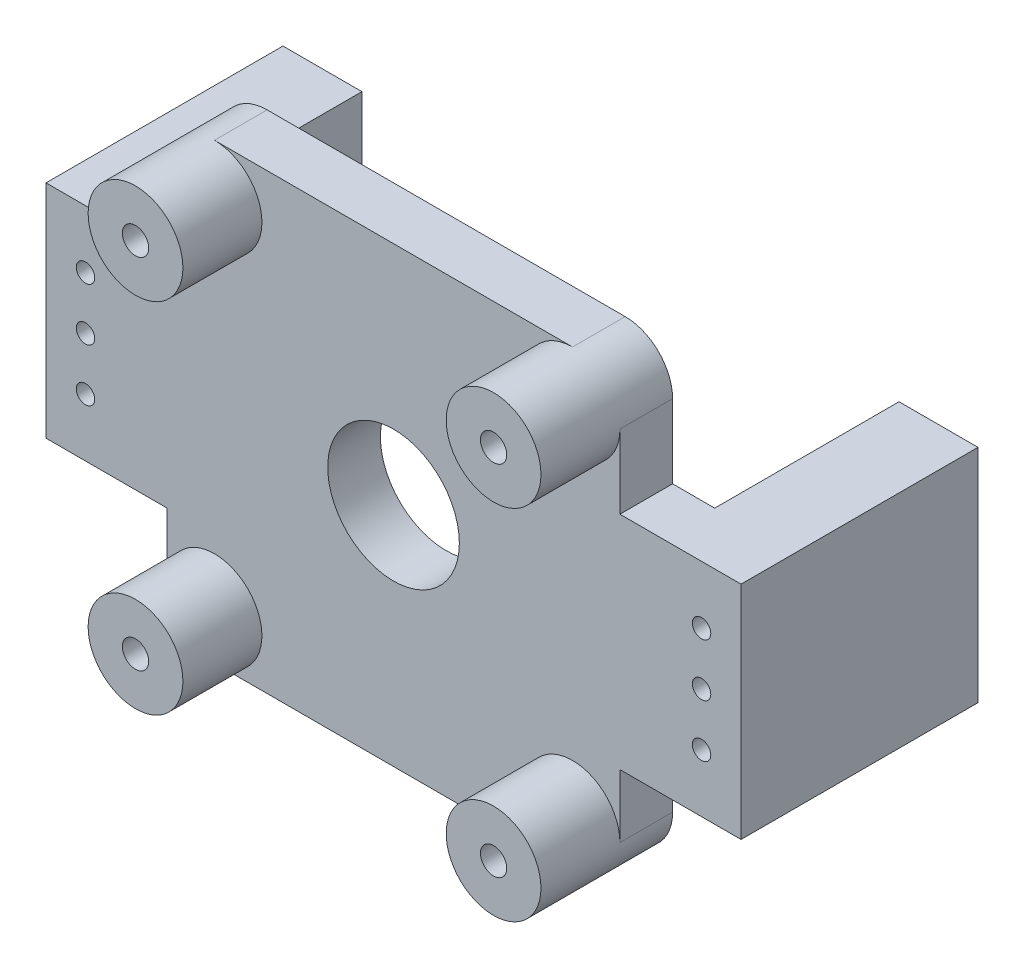
SolidWorks part; units mm, degrees
ref_plane "前视基准面" through (0, 0, 0) normal (0, 0, 1) x (1, 0, 0)
ref_plane "上视基准面" through (0, 0, 0) normal (0, 1, 0) x (1, 0, 0)
ref_plane "右视基准面" through (0, 0, 0) normal (1, 0, 0) x (0, 0, -1)
sketch "草图1" plane through (0, 0, 0) normal (0, 0, 1) x (1, 0, 0)
  line L1 (-43, 43) -> (43, 43)
  line L2 (-43, 43) -> (-43, -43)
  line L3 (-43, -43) -> (43, -43)
  line L4 (43, 43) -> (43, -43)
  circle A0 centre (-34, 34) radius 2
  circle A1 centre (34, 34) radius 2
  circle A2 centre (34, -34) radius 2
  circle A3 centre (-34, -34) radius 2
  dimension "D5" = 4
  dimension "D6" = 4
  dimension "D7" = 4
  dimension "D8" = 4
  dimension "D9" = 68
  dimension "D10" = 68
  dimension "D11" = 68
  dimension "D12" = 9
  dimension "D13" = 9
  dimension "D14" = 9
  dimension "D15" = 68
  dimension "D16" = 9
  dimension "D1" = 86
  dimension "D2" = 86
  dimension "D3" = 43
  dimension "D4" = 43
extrude "凸台-拉伸1" add sketch "草图1" along normal blind 10
fillet "圆角1" radius 5 4 edges at (-43, -43, 5) (43, -43, 5) (-43, 43, 5) (43, 43, 5)
sketch "草图2" plane through (0, 0, 10) normal (0, 0, 1) x (1, 0, 0)
  circle A0 centre (-34, 34) radius 9
  circle A1 centre (34, 34) radius 9
  circle A2 centre (34, -34) radius 9
  circle A3 centre (-34, -34) radius 9
  circle A4 centre (-34, 34) radius 2.5
  circle A5 centre (34, 34) radius 2.5
  circle A6 centre (34, -34) radius 2.5
  circle A7 centre (-34, -34) radius 2.5
  dimension "D1" = 18
  dimension "D2" = 18
  dimension "D3" = 18
  dimension "D4" = 18
  dimension "D5" = 5
  dimension "D6" = 5
  dimension "D7" = 5
  dimension "D8" = 5
extrude "凸台-拉伸2" add sketch "草图2" along normal blind 15
sketch "草图3" plane through (0, 0, 10) normal (0, 0, 1) x (1, 0, 0)
  circle A0 centre (0, 0) radius 12.5
  dimension "D1" = 25
extrude "切除-拉伸1" cut sketch "草图3" against normal blind 16
sketch "草图5" plane through (0, 0, 0) normal (0, 0, -1) x (-1, 0, 0)
  line L0 (5.7018, 29.4574) -> (7.4378, 39.3024)
  line L1 (4.717, 29.6311) -> (6.453, 39.4761)
  line L2 (0.5, 30) -> (0.5, 39.9969)
  line L3 (-0.5, 30) -> (-0.5, 39.9969)
  line L4 (4.717, 29.6311) -> (5.7018, 29.4574)
  line L5 (10.7305, 28.0198) -> (14.1496, 37.4138)
  line L6 (-0.5, 30) -> (0.5, 30)
  line L7 (9.7908, 28.3618) -> (13.2099, 37.7558)
  line L8 (9.7908, 28.3618) -> (10.7305, 28.0198)
  line L9 (15.433, 25.7308) -> (20.4315, 34.3883)
  line L10 (14.567, 26.2308) -> (19.5654, 34.8883)
  line L11 (14.567, 26.2308) -> (15.433, 25.7308)
  line L12 (19.6667, 22.6599) -> (26.0925, 30.318)
  line L13 (18.9006, 23.3027) -> (25.3265, 30.9608)
  line L14 (18.9006, 23.3027) -> (19.6667, 22.6599)
  line L15 (23.3027, 18.9006) -> (30.9608, 25.3265)
  line L16 (22.6599, 19.6667) -> (30.318, 26.0925)
  line L17 (22.6599, 19.6667) -> (23.3027, 18.9006)
  line L18 (26.2308, 14.567) -> (34.8883, 19.5654)
  line L19 (25.7308, 15.433) -> (34.3883, 20.4315)
  line L20 (25.7308, 15.433) -> (26.2308, 14.567)
  line L21 (28.3618, 9.7908) -> (37.7558, 13.2099)
  line L22 (28.0198, 10.7305) -> (37.4138, 14.1496)
  line L23 (28.0198, 10.7305) -> (28.3618, 9.7908)
  line L24 (29.6311, 4.717) -> (39.4761, 6.453)
  line L25 (29.4574, 5.7018) -> (39.3024, 7.4378)
  line L26 (29.4574, 5.7018) -> (29.6311, 4.717)
  line L27 (30, -0.5) -> (39.9969, -0.5)
  line L28 (30, 0.5) -> (39.9969, 0.5)
  line L29 (30, 0.5) -> (30, -0.5)
  line L30 (29.4574, -5.7018) -> (39.3024, -7.4378)
  line L31 (29.6311, -4.717) -> (39.4761, -6.453)
  line L32 (29.6311, -4.717) -> (29.4574, -5.7018)
  line L33 (28.0198, -10.7305) -> (37.4138, -14.1496)
  line L34 (28.3618, -9.7908) -> (37.7558, -13.2099)
  line L35 (28.3618, -9.7908) -> (28.0198, -10.7305)
  line L36 (25.7308, -15.433) -> (34.3883, -20.4315)
  line L37 (26.2308, -14.567) -> (34.8883, -19.5654)
  line L38 (26.2308, -14.567) -> (25.7308, -15.433)
  line L39 (22.6599, -19.6667) -> (30.318, -26.0925)
  line L40 (23.3027, -18.9006) -> (30.9608, -25.3265)
  line L41 (23.3027, -18.9006) -> (22.6599, -19.6667)
  line L42 (18.9006, -23.3027) -> (25.3265, -30.9608)
  line L43 (19.6667, -22.6599) -> (26.0925, -30.318)
  line L44 (19.6667, -22.6599) -> (18.9006, -23.3027)
  line L45 (14.567, -26.2308) -> (19.5654, -34.8883)
  line L46 (15.433, -25.7308) -> (20.4315, -34.3883)
  line L47 (15.433, -25.7308) -> (14.567, -26.2308)
  line L48 (9.7908, -28.3618) -> (13.2099, -37.7558)
  line L49 (10.7305, -28.0198) -> (14.1496, -37.4138)
  line L50 (10.7305, -28.0198) -> (9.7908, -28.3618)
  line L51 (4.717, -29.6311) -> (6.453, -39.4761)
  line L52 (5.7018, -29.4574) -> (7.4378, -39.3024)
  line L53 (5.7018, -29.4574) -> (4.717, -29.6311)
  line L54 (-0.5, -30) -> (-0.5, -39.9969)
  line L55 (0.5, -30) -> (0.5, -39.9969)
  line L56 (0.5, -30) -> (-0.5, -30)
  line L57 (-5.7018, -29.4574) -> (-7.4378, -39.3024)
  line L58 (-4.717, -29.6311) -> (-6.453, -39.4761)
  line L59 (-4.717, -29.6311) -> (-5.7018, -29.4574)
  line L60 (-10.7305, -28.0198) -> (-14.1496, -37.4138)
  line L61 (-9.7908, -28.3618) -> (-13.2099, -37.7558)
  line L62 (-9.7908, -28.3618) -> (-10.7305, -28.0198)
  line L63 (-15.433, -25.7308) -> (-20.4315, -34.3883)
  line L64 (-14.567, -26.2308) -> (-19.5654, -34.8883)
  line L65 (-14.567, -26.2308) -> (-15.433, -25.7308)
  line L66 (-19.6667, -22.6599) -> (-26.0925, -30.318)
  line L67 (-18.9006, -23.3027) -> (-25.3265, -30.9608)
  line L68 (-18.9006, -23.3027) -> (-19.6667, -22.6599)
  line L69 (-23.3027, -18.9006) -> (-30.9608, -25.3265)
  line L70 (-22.6599, -19.6667) -> (-30.318, -26.0925)
  line L71 (-22.6599, -19.6667) -> (-23.3027, -18.9006)
  line L72 (-26.2308, -14.567) -> (-34.8883, -19.5654)
  line L73 (-25.7308, -15.433) -> (-34.3883, -20.4315)
  line L74 (-25.7308, -15.433) -> (-26.2308, -14.567)
  line L75 (-28.3618, -9.7908) -> (-37.7558, -13.2099)
  line L76 (-28.0198, -10.7305) -> (-37.4138, -14.1496)
  line L77 (-28.0198, -10.7305) -> (-28.3618, -9.7908)
  line L78 (-29.6311, -4.717) -> (-39.4761, -6.453)
  line L79 (-29.4574, -5.7018) -> (-39.3024, -7.4378)
  line L80 (-29.4574, -5.7018) -> (-29.6311, -4.717)
  line L81 (-30, 0.5) -> (-39.9969, 0.5)
  line L82 (-30, -0.5) -> (-39.9969, -0.5)
  line L83 (-30, -0.5) -> (-30, 0.5)
  line L84 (-29.4574, 5.7018) -> (-39.3024, 7.4378)
  line L85 (-29.6311, 4.717) -> (-39.4761, 6.453)
  line L86 (-29.6311, 4.717) -> (-29.4574, 5.7018)
  line L87 (-28.0198, 10.7305) -> (-37.4138, 14.1496)
  line L88 (-28.3618, 9.7908) -> (-37.7558, 13.2099)
  line L89 (-28.3618, 9.7908) -> (-28.0198, 10.7305)
  line L90 (-25.7308, 15.433) -> (-34.3883, 20.4315)
  line L91 (-26.2308, 14.567) -> (-34.8883, 19.5654)
  line L92 (-26.2308, 14.567) -> (-25.7308, 15.433)
  line L93 (-22.6599, 19.6667) -> (-30.318, 26.0925)
  line L94 (-23.3027, 18.9006) -> (-30.9608, 25.3265)
  line L95 (-23.3027, 18.9006) -> (-22.6599, 19.6667)
  line L96 (-18.9006, 23.3027) -> (-25.3265, 30.9608)
  line L97 (-19.6667, 22.6599) -> (-26.0925, 30.318)
  line L98 (-19.6667, 22.6599) -> (-18.9006, 23.3027)
  line L99 (-14.567, 26.2308) -> (-19.5654, 34.8883)
  line L100 (-15.433, 25.7308) -> (-20.4315, 34.3883)
  line L101 (-15.433, 25.7308) -> (-14.567, 26.2308)
  line L102 (-9.7908, 28.3618) -> (-13.2099, 37.7558)
  line L103 (-10.7305, 28.0198) -> (-14.1496, 37.4138)
  line L104 (-10.7305, 28.0198) -> (-9.7908, 28.3618)
  line L105 (-4.717, 29.6311) -> (-6.453, 39.4761)
  line L106 (-5.7018, 29.4574) -> (-7.4378, 39.3024)
  line L107 (-5.7018, 29.4574) -> (-4.717, 29.6311)
  arc A0 (0.5, 39.9969) -> (-0.5, 39.9969) centre (0, 0) ccw
  arc A1 (7.4378, 39.3024) -> (6.453, 39.4761) centre (0, 0) ccw
  arc A2 (14.1496, 37.4138) -> (13.2099, 37.7558) centre (0, 0) ccw
  arc A3 (20.4315, 34.3883) -> (19.5654, 34.8883) centre (0, 0) ccw
  arc A4 (26.0925, 30.318) -> (25.3265, 30.9608) centre (0, 0) ccw
  arc A5 (30.9608, 25.3265) -> (30.318, 26.0925) centre (0, 0) ccw
  arc A6 (34.8883, 19.5654) -> (34.3883, 20.4315) centre (0, 0) ccw
  arc A7 (37.7558, 13.2099) -> (37.4138, 14.1496) centre (0, 0) ccw
  arc A8 (39.4761, 6.453) -> (39.3024, 7.4378) centre (0, 0) ccw
  arc A9 (39.9969, -0.5) -> (39.9969, 0.5) centre (0, 0) ccw
  arc A10 (39.3024, -7.4378) -> (39.4761, -6.453) centre (0, 0) ccw
  arc A11 (37.4138, -14.1496) -> (37.7558, -13.2099) centre (0, 0) ccw
  arc A12 (34.3883, -20.4315) -> (34.8883, -19.5654) centre (0, 0) ccw
  arc A13 (30.318, -26.0925) -> (30.9608, -25.3265) centre (0, 0) ccw
  arc A14 (25.3265, -30.9608) -> (26.0925, -30.318) centre (0, 0) ccw
  arc A15 (19.5654, -34.8883) -> (20.4315, -34.3883) centre (0, 0) ccw
  arc A16 (13.2099, -37.7558) -> (14.1496, -37.4138) centre (0, 0) ccw
  arc A17 (6.453, -39.4761) -> (7.4378, -39.3024) centre (0, 0) ccw
  arc A18 (-0.5, -39.9969) -> (0.5, -39.9969) centre (0, 0) ccw
  arc A19 (-7.4378, -39.3024) -> (-6.453, -39.4761) centre (0, 0) ccw
  arc A20 (-14.1496, -37.4138) -> (-13.2099, -37.7558) centre (0, 0) ccw
  arc A21 (-20.4315, -34.3883) -> (-19.5654, -34.8883) centre (0, 0) ccw
  arc A22 (-26.0925, -30.318) -> (-25.3265, -30.9608) centre (0, 0) ccw
  arc A23 (-30.9608, -25.3265) -> (-30.318, -26.0925) centre (0, 0) ccw
  arc A24 (-34.8883, -19.5654) -> (-34.3883, -20.4315) centre (0, 0) ccw
  arc A25 (-37.7558, -13.2099) -> (-37.4138, -14.1496) centre (0, 0) ccw
  arc A26 (-39.4761, -6.453) -> (-39.3024, -7.4378) centre (0, 0) ccw
  arc A27 (-39.9969, 0.5) -> (-39.9969, -0.5) centre (0, 0) ccw
  arc A28 (-39.3024, 7.4378) -> (-39.4761, 6.453) centre (0, 0) ccw
  arc A29 (-37.4138, 14.1496) -> (-37.7558, 13.2099) centre (0, 0) ccw
  arc A30 (-34.3883, 20.4315) -> (-34.8883, 19.5654) centre (0, 0) ccw
  arc A31 (-30.318, 26.0925) -> (-30.9608, 25.3265) centre (0, 0) ccw
  arc A32 (-25.3265, 30.9608) -> (-26.0925, 30.318) centre (0, 0) ccw
  arc A33 (-19.5654, 34.8883) -> (-20.4315, 34.3883) centre (0, 0) ccw
  arc A34 (-13.2099, 37.7558) -> (-14.1496, 37.4138) centre (0, 0) ccw
  arc A35 (-6.453, 39.4761) -> (-7.4378, 39.3024) centre (0, 0) ccw
  point P149 (0, 0)
  dimension "D1" = 80
  dimension "D2" = 36
extrude "凸台-拉伸3" [suppressed] add sketch "草图5" along normal blind 1
sketch "草图6" [suppressed] plane through (0, 0, 0) normal (0, 0, -1) x (-1, 0, 0)
  line L0 (2.5524, 34.9104) -> (2.9879, 39.8883)
  line L1 (8.5757, 33.9368) -> (9.869, 38.7634)
  line L2 (9.0587, 33.8074) -> (9.5416, 33.678)
  line L3 (9.5416, 33.678) -> (9.0587, 33.8074)
  line L4 (3.0505, 34.8668) -> (3.5485, 34.8232)
  line L5 (3.5485, 34.8232) -> (3.0505, 34.8668)
  line L6 (3.0505, 34.8668) -> (2.5524, 34.9104)
  line L7 (3.5485, 34.8232) -> (3.9841, 39.8011)
  line L8 (9.0587, 33.8074) -> (8.5757, 33.9368)
  line L9 (9.5416, 33.678) -> (10.8349, 38.5046)
  line L10 (14.3385, 31.9321) -> (16.4503, 36.4608)
  line L11 (14.7916, 31.7208) -> (15.2448, 31.5095)
  line L12 (15.2448, 31.5095) -> (14.7916, 31.7208)
  line L13 (14.7916, 31.7208) -> (14.3385, 31.9321)
  line L14 (15.2448, 31.5095) -> (17.3566, 36.0382)
  line L15 (19.6656, 28.9571) -> (22.5317, 33.0503)
  line L16 (20.0752, 28.6703) -> (20.4848, 28.3835)
  line L17 (20.4848, 28.3835) -> (20.0752, 28.6703)
  line L18 (20.0752, 28.6703) -> (19.6656, 28.9571)
  line L19 (20.4848, 28.3835) -> (23.3508, 32.4767)
  line L20 (24.3952, 25.1023) -> (27.9285, 28.6356)
  line L21 (24.7487, 24.7487) -> (25.1023, 24.3952)
  line L22 (25.1023, 24.3952) -> (24.7487, 24.7487)
  line L23 (24.7487, 24.7487) -> (24.3952, 25.1023)
  line L24 (25.1023, 24.3952) -> (28.6356, 27.9285)
  line L25 (28.3835, 20.4848) -> (32.4767, 23.3508)
  line L26 (28.6703, 20.0752) -> (28.9571, 19.6656)
  line L27 (28.9571, 19.6656) -> (28.6703, 20.0752)
  line L28 (28.6703, 20.0752) -> (28.3835, 20.4848)
  line L29 (28.9571, 19.6656) -> (33.0503, 22.5317)
  line L30 (31.5095, 15.2448) -> (36.0382, 17.3566)
  line L31 (31.7208, 14.7916) -> (31.9321, 14.3385)
  line L32 (31.9321, 14.3385) -> (31.7208, 14.7916)
  line L33 (31.7208, 14.7916) -> (31.5095, 15.2448)
  line L34 (31.9321, 14.3385) -> (36.4608, 16.4503)
  line L35 (33.678, 9.5416) -> (38.5046, 10.8349)
  line L36 (33.8074, 9.0587) -> (33.9368, 8.5757)
  line L37 (33.9368, 8.5757) -> (33.8074, 9.0587)
  line L38 (33.8074, 9.0587) -> (33.678, 9.5416)
  line L39 (33.9368, 8.5757) -> (38.7634, 9.869)
  line L40 (34.8232, 3.5485) -> (39.8011, 3.9841)
  line L41 (34.8668, 3.0505) -> (34.9104, 2.5524)
  line L42 (34.9104, 2.5524) -> (34.8668, 3.0505)
  line L43 (34.8668, 3.0505) -> (34.8232, 3.5485)
  line L44 (34.9104, 2.5524) -> (39.8883, 2.9879)
  line L45 (34.9104, -2.5524) -> (39.8883, -2.9879)
  line L46 (34.8668, -3.0505) -> (34.8232, -3.5485)
  line L47 (34.8232, -3.5485) -> (34.8668, -3.0505)
  line L48 (34.8668, -3.0505) -> (34.9104, -2.5524)
  line L49 (34.8232, -3.5485) -> (39.8011, -3.9841)
  line L50 (33.9368, -8.5757) -> (38.7634, -9.869)
  line L51 (33.8074, -9.0587) -> (33.678, -9.5416)
  line L52 (33.678, -9.5416) -> (33.8074, -9.0587)
  line L53 (33.8074, -9.0587) -> (33.9368, -8.5757)
  line L54 (33.678, -9.5416) -> (38.5046, -10.8349)
  line L55 (31.9321, -14.3385) -> (36.4608, -16.4503)
  line L56 (31.7208, -14.7916) -> (31.5095, -15.2448)
  line L57 (31.5095, -15.2448) -> (31.7208, -14.7916)
  line L58 (31.7208, -14.7916) -> (31.9321, -14.3385)
  line L59 (31.5095, -15.2448) -> (36.0382, -17.3566)
  line L60 (28.9571, -19.6656) -> (33.0503, -22.5317)
  line L61 (28.6703, -20.0752) -> (28.3835, -20.4848)
  line L62 (28.3835, -20.4848) -> (28.6703, -20.0752)
  line L63 (28.6703, -20.0752) -> (28.9571, -19.6656)
  line L64 (28.3835, -20.4848) -> (32.4767, -23.3508)
  line L65 (25.1023, -24.3952) -> (28.6356, -27.9285)
  line L66 (24.7487, -24.7487) -> (24.3952, -25.1023)
  line L67 (24.3952, -25.1023) -> (24.7487, -24.7487)
  line L68 (24.7487, -24.7487) -> (25.1023, -24.3952)
  line L69 (24.3952, -25.1023) -> (27.9285, -28.6356)
  line L70 (20.4848, -28.3835) -> (23.3508, -32.4767)
  line L71 (20.0752, -28.6703) -> (19.6656, -28.9571)
  line L72 (19.6656, -28.9571) -> (20.0752, -28.6703)
  line L73 (20.0752, -28.6703) -> (20.4848, -28.3835)
  line L74 (19.6656, -28.9571) -> (22.5317, -33.0503)
  line L75 (15.2448, -31.5095) -> (17.3566, -36.0382)
  line L76 (14.7916, -31.7208) -> (14.3385, -31.9321)
  line L77 (14.3385, -31.9321) -> (14.7916, -31.7208)
  line L78 (14.7916, -31.7208) -> (15.2448, -31.5095)
  line L79 (14.3385, -31.9321) -> (16.4503, -36.4608)
  line L80 (9.5416, -33.678) -> (10.8349, -38.5046)
  line L81 (9.0587, -33.8074) -> (8.5757, -33.9368)
  line L82 (8.5757, -33.9368) -> (9.0587, -33.8074)
  line L83 (9.0587, -33.8074) -> (9.5416, -33.678)
  line L84 (8.5757, -33.9368) -> (9.869, -38.7634)
  line L85 (3.5485, -34.8232) -> (3.9841, -39.8011)
  line L86 (3.0505, -34.8668) -> (2.5524, -34.9104)
  line L87 (2.5524, -34.9104) -> (3.0505, -34.8668)
  line L88 (3.0505, -34.8668) -> (3.5485, -34.8232)
  line L89 (2.5524, -34.9104) -> (2.9879, -39.8883)
  line L90 (-2.5524, -34.9104) -> (-2.9879, -39.8883)
  line L91 (-3.0505, -34.8668) -> (-3.5485, -34.8232)
  line L92 (-3.5485, -34.8232) -> (-3.0505, -34.8668)
  line L93 (-3.0505, -34.8668) -> (-2.5524, -34.9104)
  line L94 (-3.5485, -34.8232) -> (-3.9841, -39.8011)
  line L95 (-8.5757, -33.9368) -> (-9.869, -38.7634)
  line L96 (-9.0587, -33.8074) -> (-9.5416, -33.678)
  line L97 (-9.5416, -33.678) -> (-9.0587, -33.8074)
  line L98 (-9.0587, -33.8074) -> (-8.5757, -33.9368)
  line L99 (-9.5416, -33.678) -> (-10.8349, -38.5046)
  line L100 (-14.3385, -31.9321) -> (-16.4503, -36.4608)
  line L101 (-14.7916, -31.7208) -> (-15.2448, -31.5095)
  line L102 (-15.2448, -31.5095) -> (-14.7916, -31.7208)
  line L103 (-14.7916, -31.7208) -> (-14.3385, -31.9321)
  line L104 (-15.2448, -31.5095) -> (-17.3566, -36.0382)
  line L105 (-19.6656, -28.9571) -> (-22.5317, -33.0503)
  line L106 (-20.0752, -28.6703) -> (-20.4848, -28.3835)
  line L107 (-20.4848, -28.3835) -> (-20.0752, -28.6703)
  line L108 (-20.0752, -28.6703) -> (-19.6656, -28.9571)
  line L109 (-20.4848, -28.3835) -> (-23.3508, -32.4767)
  line L110 (-24.3952, -25.1023) -> (-27.9285, -28.6356)
  line L111 (-24.7487, -24.7487) -> (-25.1023, -24.3952)
  line L112 (-25.1023, -24.3952) -> (-24.7487, -24.7487)
  line L113 (-24.7487, -24.7487) -> (-24.3952, -25.1023)
  line L114 (-25.1023, -24.3952) -> (-28.6356, -27.9285)
  line L115 (-28.3835, -20.4848) -> (-32.4767, -23.3508)
  line L116 (-28.6703, -20.0752) -> (-28.9571, -19.6656)
  line L117 (-28.9571, -19.6656) -> (-28.6703, -20.0752)
  line L118 (-28.6703, -20.0752) -> (-28.3835, -20.4848)
  line L119 (-28.9571, -19.6656) -> (-33.0503, -22.5317)
  line L120 (-31.5095, -15.2448) -> (-36.0382, -17.3566)
  line L121 (-31.7208, -14.7916) -> (-31.9321, -14.3385)
  line L122 (-31.9321, -14.3385) -> (-31.7208, -14.7916)
  line L123 (-31.7208, -14.7916) -> (-31.5095, -15.2448)
  line L124 (-31.9321, -14.3385) -> (-36.4608, -16.4503)
  line L125 (-33.678, -9.5416) -> (-38.5046, -10.8349)
  line L126 (-33.8074, -9.0587) -> (-33.9368, -8.5757)
  line L127 (-33.9368, -8.5757) -> (-33.8074, -9.0587)
  line L128 (-33.8074, -9.0587) -> (-33.678, -9.5416)
  line L129 (-33.9368, -8.5757) -> (-38.7634, -9.869)
  line L130 (-34.8232, -3.5485) -> (-39.8011, -3.9841)
  line L131 (-34.8668, -3.0505) -> (-34.9104, -2.5524)
  line L132 (-34.9104, -2.5524) -> (-34.8668, -3.0505)
  line L133 (-34.8668, -3.0505) -> (-34.8232, -3.5485)
  line L134 (-34.9104, -2.5524) -> (-39.8883, -2.9879)
  line L135 (-34.9104, 2.5524) -> (-39.8883, 2.9879)
  line L136 (-34.8668, 3.0505) -> (-34.8232, 3.5485)
  line L137 (-34.8232, 3.5485) -> (-34.8668, 3.0505)
  line L138 (-34.8668, 3.0505) -> (-34.9104, 2.5524)
  line L139 (-34.8232, 3.5485) -> (-39.8011, 3.9841)
  line L140 (-33.9368, 8.5757) -> (-38.7634, 9.869)
  line L141 (-33.8074, 9.0587) -> (-33.678, 9.5416)
  line L142 (-33.678, 9.5416) -> (-33.8074, 9.0587)
  line L143 (-33.8074, 9.0587) -> (-33.9368, 8.5757)
  line L144 (-33.678, 9.5416) -> (-38.5046, 10.8349)
  line L145 (-31.9321, 14.3385) -> (-36.4608, 16.4503)
  line L146 (-31.7208, 14.7916) -> (-31.5095, 15.2448)
  line L147 (-31.5095, 15.2448) -> (-31.7208, 14.7916)
  line L148 (-31.7208, 14.7916) -> (-31.9321, 14.3385)
  line L149 (-31.5095, 15.2448) -> (-36.0382, 17.3566)
  line L150 (-28.9571, 19.6656) -> (-33.0503, 22.5317)
  line L151 (-28.6703, 20.0752) -> (-28.3835, 20.4848)
  line L152 (-28.3835, 20.4848) -> (-28.6703, 20.0752)
  line L153 (-28.6703, 20.0752) -> (-28.9571, 19.6656)
  line L154 (-28.3835, 20.4848) -> (-32.4767, 23.3508)
  line L155 (-25.1023, 24.3952) -> (-28.6356, 27.9285)
  line L156 (-24.7487, 24.7487) -> (-24.3952, 25.1023)
  line L157 (-24.3952, 25.1023) -> (-24.7487, 24.7487)
  line L158 (-24.7487, 24.7487) -> (-25.1023, 24.3952)
  line L159 (-24.3952, 25.1023) -> (-27.9285, 28.6356)
  line L160 (-20.4848, 28.3835) -> (-23.3508, 32.4767)
  line L161 (-20.0752, 28.6703) -> (-19.6656, 28.9571)
  line L162 (-19.6656, 28.9571) -> (-20.0752, 28.6703)
  line L163 (-20.0752, 28.6703) -> (-20.4848, 28.3835)
  line L164 (-19.6656, 28.9571) -> (-22.5317, 33.0503)
  line L165 (-15.2448, 31.5095) -> (-17.3566, 36.0382)
  line L166 (-14.7916, 31.7208) -> (-14.3385, 31.9321)
  line L167 (-14.3385, 31.9321) -> (-14.7916, 31.7208)
  line L168 (-14.7916, 31.7208) -> (-15.2448, 31.5095)
  line L169 (-14.3385, 31.9321) -> (-16.4503, 36.4608)
  line L170 (-9.5416, 33.678) -> (-10.8349, 38.5046)
  line L171 (-9.0587, 33.8074) -> (-8.5757, 33.9368)
  line L172 (-8.5757, 33.9368) -> (-9.0587, 33.8074)
  line L173 (-9.0587, 33.8074) -> (-9.5416, 33.678)
  line L174 (-8.5757, 33.9368) -> (-9.869, 38.7634)
  line L175 (-3.5485, 34.8232) -> (-3.9841, 39.8011)
  line L176 (-3.0505, 34.8668) -> (-2.5524, 34.9104)
  line L177 (-2.5524, 34.9104) -> (-3.0505, 34.8668)
  line L178 (-3.0505, 34.8668) -> (-3.5485, 34.8232)
  line L179 (-2.5524, 34.9104) -> (-2.9879, 39.8883)
  circle A0 centre (0, 0) radius 40
  circle A1 centre (0, 0) radius 41
  point P189 (0, 0)
  dimension "D2" = 36
  dimension "D1" = 1
extrude "凸台-拉伸4" [suppressed] add sketch "草图6" along normal blind 1 contours A1 A0 L43
sketch "草图7" plane through (0, 0, 0) normal (0, 0, -1) x (-1, 0, 0)
  line L0 (8.6331, 33.9186) -> (9.8664, 38.7641)
  line L1 (9.4828, 33.6909) -> (10.8375, 38.5039)
  line L2 (2.6121, 34.9024) -> (2.9852, 39.8884)
  line L3 (3.4883, 34.8257) -> (3.9867, 39.8008)
  line L4 (9.8664, 38.7641) -> (8.6331, 33.9186)
  line L5 (2.9852, 39.8884) -> (2.6121, 34.9024)
  line L6 (3.9867, 39.8008) -> (3.4883, 34.8257)
  line L7 (2.6121, 34.9024) -> (3.4883, 34.8257)
  line L8 (10.8375, 38.5039) -> (9.4828, 33.6909)
  line L9 (8.6331, 33.9186) -> (9.4828, 33.6909)
  line L10 (14.3919, 31.9041) -> (16.4478, 36.4619)
  line L11 (15.1891, 31.5324) -> (17.3589, 36.037)
  line L12 (16.4478, 36.4619) -> (14.3919, 31.9041)
  line L13 (17.3589, 36.037) -> (15.1891, 31.5324)
  line L14 (14.3919, 31.9041) -> (15.1891, 31.5324)
  line L15 (19.7133, 28.9203) -> (22.5295, 33.0518)
  line L16 (20.4339, 28.4158) -> (23.353, 32.4752)
  line L17 (22.5295, 33.0518) -> (19.7133, 28.9203)
  line L18 (23.353, 32.4752) -> (20.4339, 28.4158)
  line L19 (19.7133, 28.9203) -> (20.4339, 28.4158)
  line L20 (24.4358, 25.0578) -> (27.9266, 28.6375)
  line L21 (25.0578, 24.4358) -> (28.6375, 27.9266)
  line L22 (27.9266, 28.6375) -> (24.4358, 25.0578)
  line L23 (28.6375, 27.9266) -> (25.0578, 24.4358)
  line L24 (24.4358, 25.0578) -> (25.0578, 24.4358)
  line L25 (28.4158, 20.4339) -> (32.4752, 23.353)
  line L26 (28.9203, 19.7133) -> (33.0518, 22.5295)
  line L27 (32.4752, 23.353) -> (28.4158, 20.4339)
  line L28 (33.0518, 22.5295) -> (28.9203, 19.7133)
  line L29 (28.4158, 20.4339) -> (28.9203, 19.7133)
  line L30 (31.5324, 15.1891) -> (36.037, 17.3589)
  line L31 (31.9041, 14.3919) -> (36.4619, 16.4478)
  line L32 (36.037, 17.3589) -> (31.5324, 15.1891)
  line L33 (36.4619, 16.4478) -> (31.9041, 14.3919)
  line L34 (31.5324, 15.1891) -> (31.9041, 14.3919)
  line L35 (33.6909, 9.4828) -> (38.5039, 10.8375)
  line L36 (33.9186, 8.6331) -> (38.7641, 9.8664)
  line L37 (38.5039, 10.8375) -> (33.6909, 9.4828)
  line L38 (38.7641, 9.8664) -> (33.9186, 8.6331)
  line L39 (33.6909, 9.4828) -> (33.9186, 8.6331)
  line L40 (34.8257, 3.4883) -> (39.8008, 3.9867)
  line L41 (34.9024, 2.6121) -> (39.8884, 2.9852)
  line L42 (39.8008, 3.9867) -> (34.8257, 3.4883)
  line L43 (39.8884, 2.9852) -> (34.9024, 2.6121)
  line L44 (34.8257, 3.4883) -> (34.9024, 2.6121)
  line L45 (34.9024, -2.6121) -> (39.8884, -2.9852)
  line L46 (34.8257, -3.4883) -> (39.8008, -3.9867)
  line L47 (39.8884, -2.9852) -> (34.9024, -2.6121)
  line L48 (39.8008, -3.9867) -> (34.8257, -3.4883)
  line L49 (34.9024, -2.6121) -> (34.8257, -3.4883)
  line L50 (33.9186, -8.6331) -> (38.7641, -9.8664)
  line L51 (33.6909, -9.4828) -> (38.5039, -10.8375)
  line L52 (38.7641, -9.8664) -> (33.9186, -8.6331)
  line L53 (38.5039, -10.8375) -> (33.6909, -9.4828)
  line L54 (33.9186, -8.6331) -> (33.6909, -9.4828)
  line L55 (31.9041, -14.3919) -> (36.4619, -16.4478)
  line L56 (31.5324, -15.1891) -> (36.037, -17.3589)
  line L57 (36.4619, -16.4478) -> (31.9041, -14.3919)
  line L58 (36.037, -17.3589) -> (31.5324, -15.1891)
  line L59 (31.9041, -14.3919) -> (31.5324, -15.1891)
  line L60 (28.9203, -19.7133) -> (33.0518, -22.5295)
  line L61 (28.4158, -20.4339) -> (32.4752, -23.353)
  line L62 (33.0518, -22.5295) -> (28.9203, -19.7133)
  line L63 (32.4752, -23.353) -> (28.4158, -20.4339)
  line L64 (28.9203, -19.7133) -> (28.4158, -20.4339)
  line L65 (25.0578, -24.4358) -> (28.6375, -27.9266)
  line L66 (24.4358, -25.0578) -> (27.9266, -28.6375)
  line L67 (28.6375, -27.9266) -> (25.0578, -24.4358)
  line L68 (27.9266, -28.6375) -> (24.4358, -25.0578)
  line L69 (25.0578, -24.4358) -> (24.4358, -25.0578)
  line L70 (20.4339, -28.4158) -> (23.353, -32.4752)
  line L71 (19.7133, -28.9203) -> (22.5295, -33.0518)
  line L72 (23.353, -32.4752) -> (20.4339, -28.4158)
  line L73 (22.5295, -33.0518) -> (19.7133, -28.9203)
  line L74 (20.4339, -28.4158) -> (19.7133, -28.9203)
  line L75 (15.1891, -31.5324) -> (17.3589, -36.037)
  line L76 (14.3919, -31.9041) -> (16.4478, -36.4619)
  line L77 (17.3589, -36.037) -> (15.1891, -31.5324)
  line L78 (16.4478, -36.4619) -> (14.3919, -31.9041)
  line L79 (15.1891, -31.5324) -> (14.3919, -31.9041)
  line L80 (9.4828, -33.6909) -> (10.8375, -38.5039)
  line L81 (8.6331, -33.9186) -> (9.8664, -38.7641)
  line L82 (10.8375, -38.5039) -> (9.4828, -33.6909)
  line L83 (9.8664, -38.7641) -> (8.6331, -33.9186)
  line L84 (9.4828, -33.6909) -> (8.6331, -33.9186)
  line L85 (3.4883, -34.8257) -> (3.9867, -39.8008)
  line L86 (2.6121, -34.9024) -> (2.9852, -39.8884)
  line L87 (3.9867, -39.8008) -> (3.4883, -34.8257)
  line L88 (2.9852, -39.8884) -> (2.6121, -34.9024)
  line L89 (3.4883, -34.8257) -> (2.6121, -34.9024)
  line L90 (-2.6121, -34.9024) -> (-2.9852, -39.8884)
  line L91 (-3.4883, -34.8257) -> (-3.9867, -39.8008)
  line L92 (-2.9852, -39.8884) -> (-2.6121, -34.9024)
  line L93 (-3.9867, -39.8008) -> (-3.4883, -34.8257)
  line L94 (-2.6121, -34.9024) -> (-3.4883, -34.8257)
  line L95 (-8.6331, -33.9186) -> (-9.8664, -38.7641)
  line L96 (-9.4828, -33.6909) -> (-10.8375, -38.5039)
  line L97 (-9.8664, -38.7641) -> (-8.6331, -33.9186)
  line L98 (-10.8375, -38.5039) -> (-9.4828, -33.6909)
  line L99 (-8.6331, -33.9186) -> (-9.4828, -33.6909)
  line L100 (-14.3919, -31.9041) -> (-16.4478, -36.4619)
  line L101 (-15.1891, -31.5324) -> (-17.3589, -36.037)
  line L102 (-16.4478, -36.4619) -> (-14.3919, -31.9041)
  line L103 (-17.3589, -36.037) -> (-15.1891, -31.5324)
  line L104 (-14.3919, -31.9041) -> (-15.1891, -31.5324)
  line L105 (-19.7133, -28.9203) -> (-22.5295, -33.0518)
  line L106 (-20.4339, -28.4158) -> (-23.353, -32.4752)
  line L107 (-22.5295, -33.0518) -> (-19.7133, -28.9203)
  line L108 (-23.353, -32.4752) -> (-20.4339, -28.4158)
  line L109 (-19.7133, -28.9203) -> (-20.4339, -28.4158)
  line L110 (-24.4358, -25.0578) -> (-27.9266, -28.6375)
  line L111 (-25.0578, -24.4358) -> (-28.6375, -27.9266)
  line L112 (-27.9266, -28.6375) -> (-24.4358, -25.0578)
  line L113 (-28.6375, -27.9266) -> (-25.0578, -24.4358)
  line L114 (-24.4358, -25.0578) -> (-25.0578, -24.4358)
  line L115 (-28.4158, -20.4339) -> (-32.4752, -23.353)
  line L116 (-28.9203, -19.7133) -> (-33.0518, -22.5295)
  line L117 (-32.4752, -23.353) -> (-28.4158, -20.4339)
  line L118 (-33.0518, -22.5295) -> (-28.9203, -19.7133)
  line L119 (-28.4158, -20.4339) -> (-28.9203, -19.7133)
  line L120 (-31.5324, -15.1891) -> (-36.037, -17.3589)
  line L121 (-31.9041, -14.3919) -> (-36.4619, -16.4478)
  line L122 (-36.037, -17.3589) -> (-31.5324, -15.1891)
  line L123 (-36.4619, -16.4478) -> (-31.9041, -14.3919)
  line L124 (-31.5324, -15.1891) -> (-31.9041, -14.3919)
  line L125 (-33.6909, -9.4828) -> (-38.5039, -10.8375)
  line L126 (-33.9186, -8.6331) -> (-38.7641, -9.8664)
  line L127 (-38.5039, -10.8375) -> (-33.6909, -9.4828)
  line L128 (-38.7641, -9.8664) -> (-33.9186, -8.6331)
  line L129 (-33.6909, -9.4828) -> (-33.9186, -8.6331)
  line L130 (-34.8257, -3.4883) -> (-39.8008, -3.9867)
  line L131 (-34.9024, -2.6121) -> (-39.8884, -2.9852)
  line L132 (-39.8008, -3.9867) -> (-34.8257, -3.4883)
  line L133 (-39.8884, -2.9852) -> (-34.9024, -2.6121)
  line L134 (-34.8257, -3.4883) -> (-34.9024, -2.6121)
  line L135 (-34.9024, 2.6121) -> (-39.8884, 2.9852)
  line L136 (-34.8257, 3.4883) -> (-39.8008, 3.9867)
  line L137 (-39.8884, 2.9852) -> (-34.9024, 2.6121)
  line L138 (-39.8008, 3.9867) -> (-34.8257, 3.4883)
  line L139 (-34.9024, 2.6121) -> (-34.8257, 3.4883)
  line L140 (-33.9186, 8.6331) -> (-38.7641, 9.8664)
  line L141 (-33.6909, 9.4828) -> (-38.5039, 10.8375)
  line L142 (-38.7641, 9.8664) -> (-33.9186, 8.6331)
  line L143 (-38.5039, 10.8375) -> (-33.6909, 9.4828)
  line L144 (-33.9186, 8.6331) -> (-33.6909, 9.4828)
  line L145 (-31.9041, 14.3919) -> (-36.4619, 16.4478)
  line L146 (-31.5324, 15.1891) -> (-36.037, 17.3589)
  line L147 (-36.4619, 16.4478) -> (-31.9041, 14.3919)
  line L148 (-36.037, 17.3589) -> (-31.5324, 15.1891)
  line L149 (-31.9041, 14.3919) -> (-31.5324, 15.1891)
  line L150 (-28.9203, 19.7133) -> (-33.0518, 22.5295)
  line L151 (-28.4158, 20.4339) -> (-32.4752, 23.353)
  line L152 (-33.0518, 22.5295) -> (-28.9203, 19.7133)
  line L153 (-32.4752, 23.353) -> (-28.4158, 20.4339)
  line L154 (-28.9203, 19.7133) -> (-28.4158, 20.4339)
  line L155 (-25.0578, 24.4358) -> (-28.6375, 27.9266)
  line L156 (-24.4358, 25.0578) -> (-27.9266, 28.6375)
  line L157 (-28.6375, 27.9266) -> (-25.0578, 24.4358)
  line L158 (-27.9266, 28.6375) -> (-24.4358, 25.0578)
  line L159 (-25.0578, 24.4358) -> (-24.4358, 25.0578)
  line L160 (-20.4339, 28.4158) -> (-23.353, 32.4752)
  line L161 (-19.7133, 28.9203) -> (-22.5295, 33.0518)
  line L162 (-23.353, 32.4752) -> (-20.4339, 28.4158)
  line L163 (-22.5295, 33.0518) -> (-19.7133, 28.9203)
  line L164 (-20.4339, 28.4158) -> (-19.7133, 28.9203)
  line L165 (-15.1891, 31.5324) -> (-17.3589, 36.037)
  line L166 (-14.3919, 31.9041) -> (-16.4478, 36.4619)
  line L167 (-17.3589, 36.037) -> (-15.1891, 31.5324)
  line L168 (-16.4478, 36.4619) -> (-14.3919, 31.9041)
  line L169 (-15.1891, 31.5324) -> (-14.3919, 31.9041)
  line L170 (-9.4828, 33.6909) -> (-10.8375, 38.5039)
  line L171 (-8.6331, 33.9186) -> (-9.8664, 38.7641)
  line L172 (-10.8375, 38.5039) -> (-9.4828, 33.6909)
  line L173 (-9.8664, 38.7641) -> (-8.6331, 33.9186)
  line L174 (-9.4828, 33.6909) -> (-8.6331, 33.9186)
  line L175 (-3.4883, 34.8257) -> (-3.9867, 39.8008)
  line L176 (-2.6121, 34.9024) -> (-2.9852, 39.8884)
  line L177 (-3.9867, 39.8008) -> (-3.4883, 34.8257)
  line L178 (-2.9852, 39.8884) -> (-2.6121, 34.9024)
  line L179 (-3.4883, 34.8257) -> (-2.6121, 34.9024)
  arc A0 (10.8375, 38.5039) -> (9.8664, 38.7641) centre (0, 0) ccw
  arc A1 (3.9867, 39.8008) -> (2.9852, 39.8884) centre (0, 0) ccw
  arc A2 (17.3589, 36.037) -> (16.4478, 36.4619) centre (0, 0) ccw
  arc A3 (23.353, 32.4752) -> (22.5295, 33.0518) centre (0, 0) ccw
  arc A4 (28.6375, 27.9266) -> (27.9266, 28.6375) centre (0, 0) ccw
  arc A5 (33.0518, 22.5295) -> (32.4752, 23.353) centre (0, 0) ccw
  arc A6 (36.4619, 16.4478) -> (36.037, 17.3589) centre (0, 0) ccw
  arc A7 (38.7641, 9.8664) -> (38.5039, 10.8375) centre (0, 0) ccw
  arc A8 (39.8884, 2.9852) -> (39.8008, 3.9867) centre (0, 0) ccw
  arc A9 (39.8008, -3.9867) -> (39.8884, -2.9852) centre (0, 0) ccw
  arc A10 (38.5039, -10.8375) -> (38.7641, -9.8664) centre (0, 0) ccw
  arc A11 (36.037, -17.3589) -> (36.4619, -16.4478) centre (0, 0) ccw
  arc A12 (32.4752, -23.353) -> (33.0518, -22.5295) centre (0, 0) ccw
  arc A13 (27.9266, -28.6375) -> (28.6375, -27.9266) centre (0, 0) ccw
  arc A14 (22.5295, -33.0518) -> (23.353, -32.4752) centre (0, 0) ccw
  arc A15 (16.4478, -36.4619) -> (17.3589, -36.037) centre (0, 0) ccw
  arc A16 (9.8664, -38.7641) -> (10.8375, -38.5039) centre (0, 0) ccw
  arc A17 (2.9852, -39.8884) -> (3.9867, -39.8008) centre (0, 0) ccw
  arc A18 (-3.9867, -39.8008) -> (-2.9852, -39.8884) centre (0, 0) ccw
  arc A19 (-10.8375, -38.5039) -> (-9.8664, -38.7641) centre (0, 0) ccw
  arc A20 (-17.3589, -36.037) -> (-16.4478, -36.4619) centre (0, 0) ccw
  arc A21 (-23.353, -32.4752) -> (-22.5295, -33.0518) centre (0, 0) ccw
  arc A22 (-28.6375, -27.9266) -> (-27.9266, -28.6375) centre (0, 0) ccw
  arc A23 (-33.0518, -22.5295) -> (-32.4752, -23.353) centre (0, 0) ccw
  arc A24 (-36.4619, -16.4478) -> (-36.037, -17.3589) centre (0, 0) ccw
  arc A25 (-38.7641, -9.8664) -> (-38.5039, -10.8375) centre (0, 0) ccw
  arc A26 (-39.8884, -2.9852) -> (-39.8008, -3.9867) centre (0, 0) ccw
  arc A27 (-39.8008, 3.9867) -> (-39.8884, 2.9852) centre (0, 0) ccw
  arc A28 (-38.5039, 10.8375) -> (-38.7641, 9.8664) centre (0, 0) ccw
  arc A29 (-36.037, 17.3589) -> (-36.4619, 16.4478) centre (0, 0) ccw
  arc A30 (-32.4752, 23.353) -> (-33.0518, 22.5295) centre (0, 0) ccw
  arc A31 (-27.9266, 28.6375) -> (-28.6375, 27.9266) centre (0, 0) ccw
  arc A32 (-22.5295, 33.0518) -> (-23.353, 32.4752) centre (0, 0) ccw
  arc A33 (-16.4478, 36.4619) -> (-17.3589, 36.037) centre (0, 0) ccw
  arc A34 (-9.8664, 38.7641) -> (-10.8375, 38.5039) centre (0, 0) ccw
  arc A35 (-2.9852, 39.8884) -> (-3.9867, 39.8008) centre (0, 0) ccw
  point P149 (0, 0)
  dimension "D1" = 36
  dimension "D4" = 5
  dimension "D5" = 5
extrude "凸台-拉伸6" [suppressed] add sketch "草图7" along normal blind 1 contours L171 A34 L170 L174 | L176 A35 L175 L179 | L3 A1 L2 L7 | L1 A0 L0 L9 | L11 A2 L10 L14 | L16 A3 L15 L19 | L21 A4 L20 L24 | L26 A5 L25 L29 | L31 A6 L30 L34 | L36 A7 L35 L39 | L41 A8 L40 L44 | L46 A9 L45 L49 | L51 A10 L50 L54 | L56 A11 L55 L59 | L61 A12 L60 L64 | L66 A13 L65 L69 | L71 A14 L70 L74 | L76 A15 L75 L79 | L81 A16 L80 L84 | L86 A17 L85 L89 | L91 A18 L90 L94 | L96 A19 L95 L99 | L101 A20 L100 L104 | L106 A21 L105 L109 | L111 A22 L110 L114 | L116 A23 L115 L119 | L121 A24 L120 L124 | L126 A25 L125 L129 | L131 A26 L130 L134 | L136 A27 L135 L139 | L141 A28 L140 L144 | L146 A29 L145 L149 | L151 A30 L150 L154 | L156 A31 L155 L159 | L161 A32 L160 L164 | L166 A33 L165 L169
sketch "草图8" plane through (0, 0, 0) normal (0, 0, -1) x (-1, 0, 0)
  line L1 (-66, 20) -> (-56, 20)
  line L2 (-66, 20) -> (-66, -22)
  line L3 (-66, -22) -> (-56, -22)
  line L4 (-56, 20) -> (-56, -22)
  line L6 (66, 20) -> (56, 20)
  line L7 (66, 20) -> (66, -22)
  line L8 (66, -22) -> (56, -22)
  line L9 (56, 20) -> (56, -22)
  point P12 (-33, -1.7699)
  point P15 (33, -2.5824)
  dimension "D1" = 10
  dimension "D2" = 42
  dimension "D3" = 20
  dimension "D4" = 10
  dimension "D5" = 42
  dimension "D6" = 22
  dimension "D7" = 56
extrude "凸台-拉伸7" add sketch "草图8" along normal blind 35 separate body
sketch "草图9" plane through (0, 0, 0) normal (0, 0, 1) x (1, 0, 0)
  line L0 (-43, 38) -> (-43, 34) construction
  line L1 (-66, 20) -> (-43, 20)
  line L2 (-66, 20) -> (-66, -22)
  line L3 (-66, -22) -> (-43, -22)
  line L4 (-43, 20) -> (-43, -22)
  line L5 (43, -38) -> (43, -34) construction
  line L6 (66, 20) -> (43, 20)
  line L7 (66, 20) -> (66, -22)
  line L8 (66, -22) -> (43, -22)
  line L9 (43, 20) -> (43, -22)
extrude "凸台-拉伸8" add sketch "草图9" along normal blind 10
sketch "草图10" plane through (0, 0, 10) normal (0, 0, 1) x (1, 0, 0)
  line L0 (34, 43) -> (43, 43)
  line L1 (-43, 43) -> (-34, 43)
  line L2 (-43, 43) -> (-43, 34)
  line L3 (-43, -43) -> (-34, -43)
  line L4 (43, 43) -> (43, 34)
  line L5 (-43, -34) -> (-43, -43)
  line L6 (34, -43) -> (43, -43)
  line L7 (43, -34) -> (43, -43)
  arc A0 (-34, 43) -> (-43, 34) centre (-34, 34) ccw
  arc A1 (43, 34) -> (34, 43) centre (34, 34) ccw
  arc A2 (34, -43) -> (43, -34) centre (34, -34) ccw
  arc A3 (-43, -34) -> (-34, -43) centre (-34, -34) ccw
extrude "切除-拉伸2" cut sketch "草图10" against normal blind 10
sketch "草图11" plane through (56, 0, 0) normal (-1, 0, 0) x (0, 0, 1)
  line L1 (-35, 20) -> (0, 20)
  line L2 (-35, 20) -> (-35, -22)
  line L3 (-35, -22) -> (0, -22)
  line L4 (0, 20) -> (0, -22)
extrude "凸台-拉伸9" add sketch "草图11" along normal blind 5
sketch "草图12" plane through (-56, 0, 0) normal (1, 0, 0) x (0, 0, -1)
  line L1 (35, 20) -> (0, 20)
  line L2 (35, 20) -> (35, -22)
  line L3 (35, -22) -> (0, -22)
  line L4 (0, 20) -> (0, -22)
extrude "凸台-拉伸10" add sketch "草图12" along normal blind 5
sketch "草图13" plane through (0, 0, -35) normal (0, 0, -1) x (-1, 0, 0)
  line L1 (51, -22) -> (66, -22) construction
  line L2 (66, 20) -> (51, 20) construction
  line L3 (66, -22) -> (66, 20) construction
  line L4 (0, 0) -> (0, -58.0115)
  circle A0 centre (58.5, 9) radius 1.75
  circle A1 centre (58.5, -1) radius 1.75
  circle A2 centre (58.5, -11) radius 1.75
  circle A3 centre (-58.5, -11) radius 1.75
  circle A4 centre (-58.5, -1) radius 1.75
  circle A5 centre (-58.5, 9) radius 1.75
  point P8 (58.5, -22)
  dimension "D1" = 3.5
  dimension "D2" = 3.5
  dimension "D3" = 3.5
  dimension "D4" = 11
  dimension "D5" = 10
  dimension "D6" = 10
  dimension "D7" = 7.5
  dimension "D8" = 7.5
  dimension "D9" = 7.5
extrude "切除-拉伸3" cut sketch "草图13" against normal blind 45 contours A5 | A4 | A3 | A0 | A1 | A2
